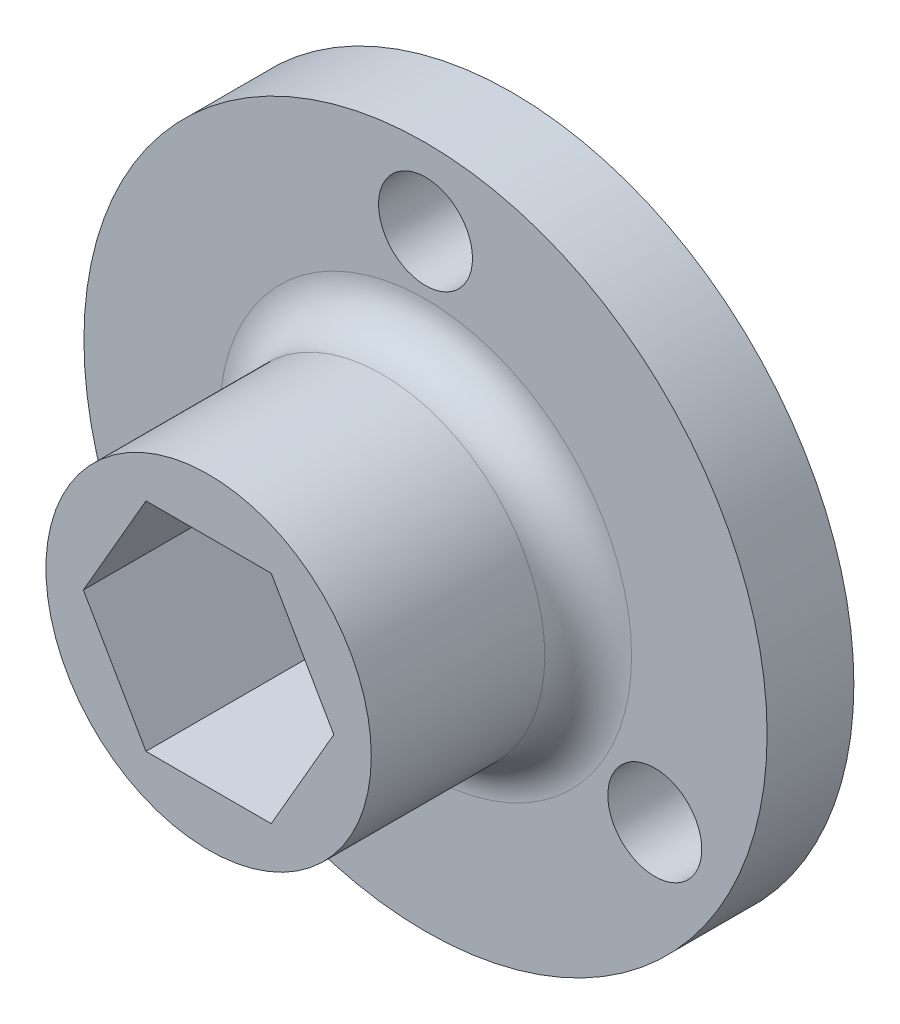
SolidWorks part; units mm, degrees
material "6061-T6 (SS)"
ref_plane "Front Plane" through (0, 0, 0) normal (0, 0, 1) x (1, 0, 0)
ref_plane "Top Plane" through (0, 0, 0) normal (0, 1, 0) x (1, 0, 0)
ref_plane "Right Plane" through (0, 0, 0) normal (1, 0, 0) x (0, 0, -1)
sketch "Sketch1" plane through (0, 0, 0) normal (0, 0, 1) x (1, 0, 0)
  circle A0 centre (0, 0) radius 20
  dimension "D1" = 40
extrude "Boss-Extrude1" add sketch "Sketch1" along normal blind 5.08
sketch "Sketch2" plane through (0, 0, 5.08) normal (0, 0, 1) x (1, 0, 0)
  circle A0 centre (0, 0) radius 9.525
  dimension "D1" = 19.05
extrude "Boss-Extrude2" add sketch "Sketch2" along normal blind 12.7
hole_wizard "M5 Clearance Hole1" positions "Sketch3" profile "Sketch4" hole size "M5" standard "ANSI Metric" end condition through all
sketch "Sketch3" plane through (0, 0, 5.08) normal (0, 0, 1) x (1, 0, 0)
  line L0 (0, 0) -> (0, 15.5) construction
  line L1 (0, 0) -> (0, 15.5) construction
  circle A0 centre (0, 0) radius 15.5 construction
  circle A1 centre (0, 0) radius 15.5 construction
  circle A2 centre (0, 0) radius 15.5 construction
  point P0 (0, 15.5)
  point P13 (13.4234, -7.75)
  point P15 (-13.4234, -7.75)
  point P24 (13.4234, -7.75)
  point P25 (-13.4234, -7.75)
  dimension "D3" = 3
  dimension "D4" = 15.5
  dimension "D2" = 3
sketch "Sketch4" plane through (0, 15.5, 5.08) normal (1, 0, 0) x (0, -1, 0)
  line L0 (0, 0) -> (0, 5.08)
  line L1 (0, 5.08) -> (2.75, 5.08)
  line L2 (2.75, 5.08) -> (2.75, 0)
  line L5 (2.75, 0) -> (0, 0)
  line L11 (0, -6.35) -> (0, 107.95) construction
  dimension "Thru Hole Dia." = 5.5
  dimension "Thru Hole Depth" = 5.08
sketch "Sketch5" plane through (0, 0, 17.78) normal (0, 0, 1) x (1, 0, 0)
  line L5 (3.6662, 6.35) -> (-3.6662, 6.35)
  line L6 (-3.6662, 6.35) -> (-7.3323, 0)
  line L7 (-7.3323, 0) -> (-3.6662, -6.35)
  line L8 (-3.6662, -6.35) -> (3.6662, -6.35)
  line L9 (3.6662, -6.35) -> (7.3323, 0)
  line L10 (7.3323, 0) -> (3.6662, 6.35)
  circle A1 centre (0, 0) radius 6.35 construction
  point P1 (0, 6.35)
  dimension "D1" = 6.35
extrude "Cut-Extrude1" cut sketch "Sketch5" against normal through all
fillet "Fillet1" radius 2.54 1 edges at (9.525, 0, 5.08)
